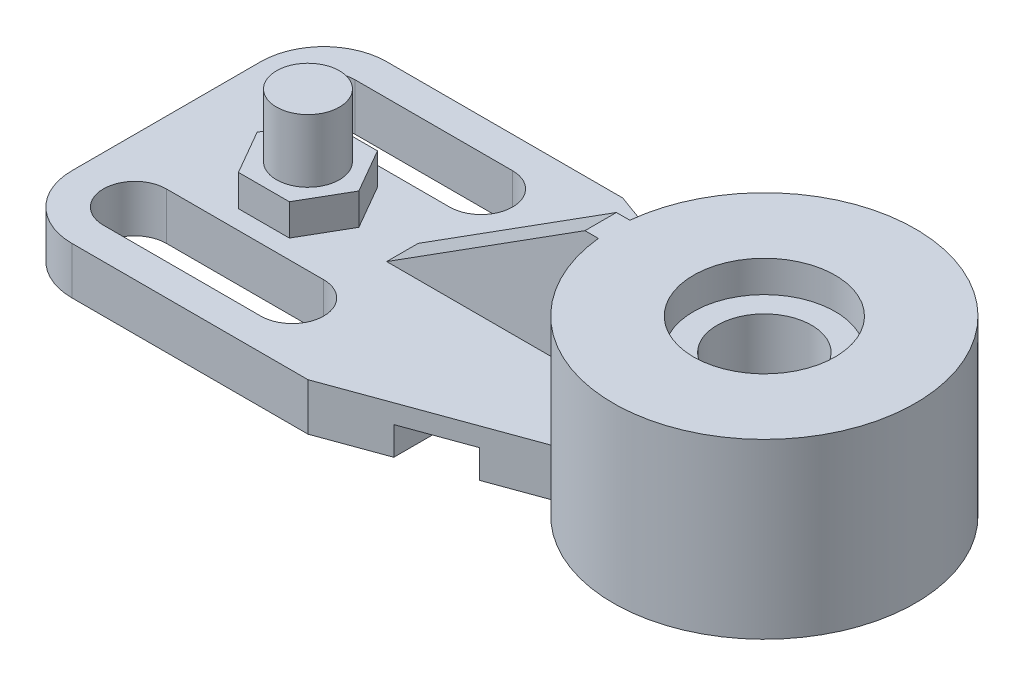
SolidWorks part; units mm, degrees
material "6061 Alloy"
ref_plane "Front Plane" through (0, 0, 0) normal (0, 0, 1) x (1, 0, 0)
ref_plane "Top Plane" through (0, 0, 0) normal (0, 1, 0) x (1, 0, 0)
ref_plane "Right Plane" through (0, 0, 0) normal (1, 0, 0) x (0, 0, -1)
sketch "Sketch2" plane through (0, 0, 0) normal (0, 0, 1) x (1, 0, 0)
  line L0 (0, 0) -> (0, 9.525)
  line L1 (0, 9.525) -> (-120.65, 9.525)
  line L2 (-120.65, 9.525) -> (-120.65, 0)
  line L3 (-120.65, 0) -> (-47.625, 0)
  line L4 (-47.625, 0) -> (-47.625, 5.715)
  line L5 (-47.625, 5.715) -> (-34.925, 5.715)
  line L6 (-34.925, 5.715) -> (-34.925, 0)
  line L7 (-34.925, 0) -> (0, 0)
  dimension "D1" = 120.65
  dimension "D2" = 9.525
  dimension "D3" = 73.025
  dimension "D4" = 12.7
  dimension "D5" = 5.715
extrude "Boss-Extrude1" add sketch "Sketch2" along normal mid plane 63.5
fillet "Fillet1" radius 12.7 2 edges at (-120.65, 4.7625, -31.75) (-120.65, 4.7625, 31.75)
sketch "Sketch3" plane through (0, 9.525, 0) normal (0, 1, 0) x (1, 0, 0)
  line L0 (-107.95, 19.05) -> (-76.2, 19.05) construction
  line L1 (-107.95, 25.4) -> (-76.2, 25.4)
  line L2 (-107.95, 12.7) -> (-76.2, 12.7)
  line L3 (-120.65, -19.05) -> (-120.65, 19.05) construction
  line L4 (-5.2388, 0) -> (5.2388, 0) construction
  line L5 (-107.95, -19.05) -> (-76.2, -19.05) construction
  line L6 (-107.95, -25.4) -> (-76.2, -25.4)
  line L7 (-107.95, -12.7) -> (-76.2, -12.7)
  arc A0 (-107.95, 25.4) -> (-107.95, 12.7) centre (-107.95, 19.05) ccw
  arc A1 (-76.2, 12.7) -> (-76.2, 25.4) centre (-76.2, 19.05) ccw
  arc A2 (-107.95, -25.4) -> (-107.95, -12.7) centre (-107.95, -19.05) cw
  arc A3 (-76.2, -12.7) -> (-76.2, -25.4) centre (-76.2, -19.05) cw
  point P2 (-92.075, 19.05)
  point P12 (-66.1789, 19.0948)
  point P13 (-118.8832, 22.4342)
  point P16 (-92.075, -19.05)
  dimension "D1" = 44.45
  dimension "D2" = 12.7
  dimension "D3" = 19.05
  dimension "D4" = 12.7
extrude "Cut-Extrude1" cut sketch "Sketch3" against normal blind 63.5
sketch "Sketch5" plane through (0, 0, 0) normal (0, 1, 0) x (1, 0, 0)
  circle A0 centre (0, 0) radius 30.48
  dimension "D1" = 60.96
extrude "Boss-Extrude2" add sketch "Sketch5" along normal blind 34.925
sketch "Sketch6" plane through (0, 34.925, 0) normal (0, 1, 0) x (1, 0, 0)
  circle A0 centre (0, 0) radius 9.525
  dimension "D1" = 19.05
extrude "Cut-Extrude2" cut sketch "Sketch6" against normal through all
sketch "Sketch7" plane through (0, 34.925, 0) normal (0, 1, 0) x (1, 0, 0)
  circle A0 centre (0, 0) radius 14.2875
  dimension "D1" = 28.575
extrude "Cut-Extrude3" cut sketch "Sketch7" against normal blind 6.35
sketch "Sketch8" plane through (0, 9.525, 0) normal (0, 1, 0) x (1, 0, 0)
  line L0 (-60.325, 31.75) -> (-24.1575, 18.5861)
  line L1 (0, 31.75) -> (-107.95, 31.75) construction
  line L2 (-120.65, -19.05) -> (-120.65, 19.05) construction
  line L4 (0, 30.48) -> (0, 31.75) construction
  line L5 (0, 30.48) -> (0, 31.75)
  line L6 (0, 31.75) -> (-60.325, 31.75)
  line L7 (-19.2087, 0) -> (19.2087, 0) construction
  line L8 (0, -31.75) -> (-60.325, -31.75)
  line L9 (0, -30.48) -> (0, -31.75)
  line L10 (-60.325, -31.75) -> (-24.1575, -18.5861)
  arc A0 (0, 30.48) -> (0, -30.48) centre (0, 0) ccw construction
  circle A1 centre (0, 0) radius 30.48 construction
  arc A2 (0, 30.48) -> (-24.1575, 18.5861) centre (0, 0) ccw
  arc A3 (0, -30.48) -> (-24.1575, -18.5861) centre (0, 0) cw
  dimension "D1" = 160
  dimension "D2" = 60.325
extrude "Cut-Extrude4" cut sketch "Sketch8" against normal through all
sketch "Sketch9" plane through (0, 0, 0) normal (0, 0, 1) x (1, 0, 0)
  line L0 (-73.025, 9.525) -> (-33.02, 34.925)
  line L1 (-60.325, 9.525) -> (-107.95, 9.525) construction
  line L2 (-33.02, 34.925) -> (-28.575, 34.925)
  line L3 (-28.575, 34.925) -> (-28.575, 9.525)
  line L4 (-28.575, 9.525) -> (-73.025, 9.525)
  line L5 (-120.65, 0) -> (-120.65, 9.525) construction
  line L6 (30.48, 34.925) -> (-30.48, 34.925) construction
  point P11 (0, 0)
  point P12 (0, 0)
  point P13 (0, 0)
  dimension "D1" = 33.02
  dimension "D2" = 47.625
  dimension "D3" = 44.45
extrude "Boss-Extrude6" add sketch "Sketch9" along normal mid plane 6.35
sketch "Sketch10" plane through (0, 9.525, 0) normal (0, 1, 0) x (1, 0, 0)
  line L0 (-107.95, 12.7) -> (-76.2, 12.7) construction
  line L1 (-81.8097, 0) -> (-86.9424, 8.89)
  line L2 (-86.9424, 8.89) -> (-97.2076, 8.89)
  line L3 (-97.2076, 8.89) -> (-102.3403, 0)
  line L4 (-102.3403, 0) -> (-97.2076, -8.89)
  line L5 (-97.2076, -8.89) -> (-86.9424, -8.89)
  line L6 (-86.9424, -8.89) -> (-81.8097, 0)
  line L7 (-60.325, 31.75) -> (-107.95, 31.75) construction
  line L8 (-120.65, -19.05) -> (-120.65, 19.05) construction
  circle A0 centre (-92.075, 0) radius 8.89 construction
  point P10 (-92.075, 12.7)
  dimension "D1" = 17.78
  dimension "D2" = 31.75
extrude "Boss-Extrude7" add sketch "Sketch10" along normal blind 6.35
sketch "Sketch11" plane through (0, 15.875, 0) normal (0, 1, 0) x (1, 0, 0)
  line L0 (-120.65, -19.05) -> (-120.65, 19.05) construction
  circle A0 centre (-92.075, 0) radius 6.35
  point P4 (-120.65, 0)
  dimension "D1" = 28.575
  dimension "D2" = 12.7
extrude "Boss-Extrude8" add sketch "Sketch11" along normal blind 12.7
